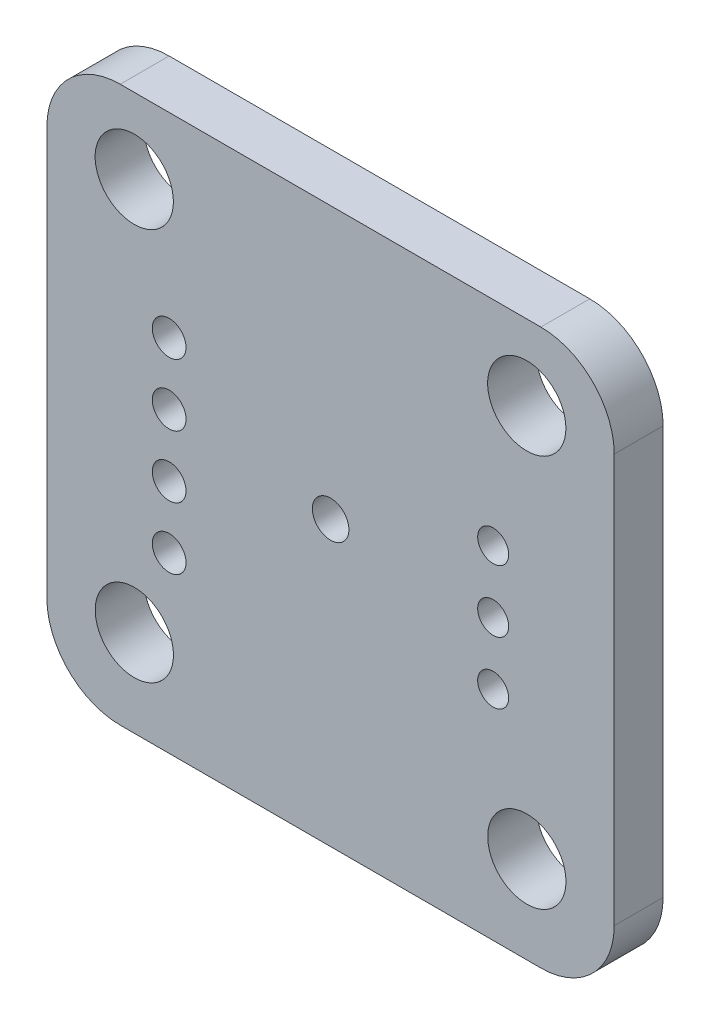
SolidWorks part; units mm, degrees
ref_plane "Front Plane" through (0, 0, 0) normal (0, 0, 1) x (1, 0, 0)
ref_plane "Top Plane" through (0, 0, 0) normal (0, 1, 0) x (1, 0, 0)
ref_plane "Right Plane" through (0, 0, 0) normal (1, 0, 0) x (0, 0, -1)
sketch "Sketch1" plane through (0, 0, 0) normal (0, 0, 1) x (1, 0, 0)
  line L2 (-11.6029, 11.1029) -> (11.5971, 11.1029)
  line L3 (-11.6029, 11.1029) -> (-11.6029, -11.5971)
  line L4 (-11.6029, -11.5971) -> (11.5971, -11.5971)
  line L5 (11.5971, 11.1029) -> (11.5971, -11.5971)
  line L6 (-0.0029, -11.5971) -> (-0.0029, 11.1029) construction
  line L7 (-11.6029, -0.2471) -> (11.5971, -0.2471) construction
  circle A0 centre (-8.0298, 8.0242) radius 1.6
  circle A1 centre (8.0213, 8.0269) radius 1.6
  circle A2 centre (8.024, -8.0242) radius 1.6
  circle A3 centre (-8.0271, -8.0269) radius 1.6
  point P2 (-0.0029, 0)
  point P7 (-0.0029, -0.2471)
  dimension "D3" = 3.2
  dimension "D1" = 23.2
  dimension "D2" = 22.7
extrude "Boss-Extrude1" add sketch "Sketch1" along normal blind 2
fillet "Fillet1" radius 3 4 edges at (11.5971, -11.5971, 1) (-11.6029, -11.5971, 1) (-11.6029, 11.1029, 1) (11.5971, 11.1029, 1)
sketch "Sketch2" plane through (0, 0, 2) normal (0, 0, 1) x (1, 0, 0)
  line L0 (-11.6029, 8.1029) -> (-11.6029, -8.5971) construction
  line L1 (-8.6029, -11.5971) -> (8.5971, -11.5971) construction
  line L2 (11.5971, -8.5971) -> (11.5971, 8.1029) construction
  circle A0 centre (6.6471, -2.6971) radius 0.6336
  circle A1 centre (6.6471, -0.1571) radius 0.6336
  circle A2 centre (6.6471, 2.3829) radius 0.6336
  circle A3 centre (-6.6029, -4.4971) radius 0.6903
  circle A4 centre (-6.6029, -1.9571) radius 0.6903
  circle A5 centre (-6.6029, 0.5829) radius 0.6903
  circle A6 centre (-6.6029, 3.1229) radius 0.6903
  dimension "D1" = 3
  dimension "D2" = 4
  dimension "D3" = 5
  dimension "D4" = 7.1
  dimension "D5" = 8.9
  dimension "D6" = 4.95
extrude "Cut-Extrude1" cut sketch "Sketch2" against normal through all
sketch "Sketch3" plane through (0, 0, 2) normal (0, 0, 1) x (1, 0, 0)
  circle A0 centre (0, 0) radius 0.7468
extrude "Cut-Extrude2" cut sketch "Sketch3" against normal through all
